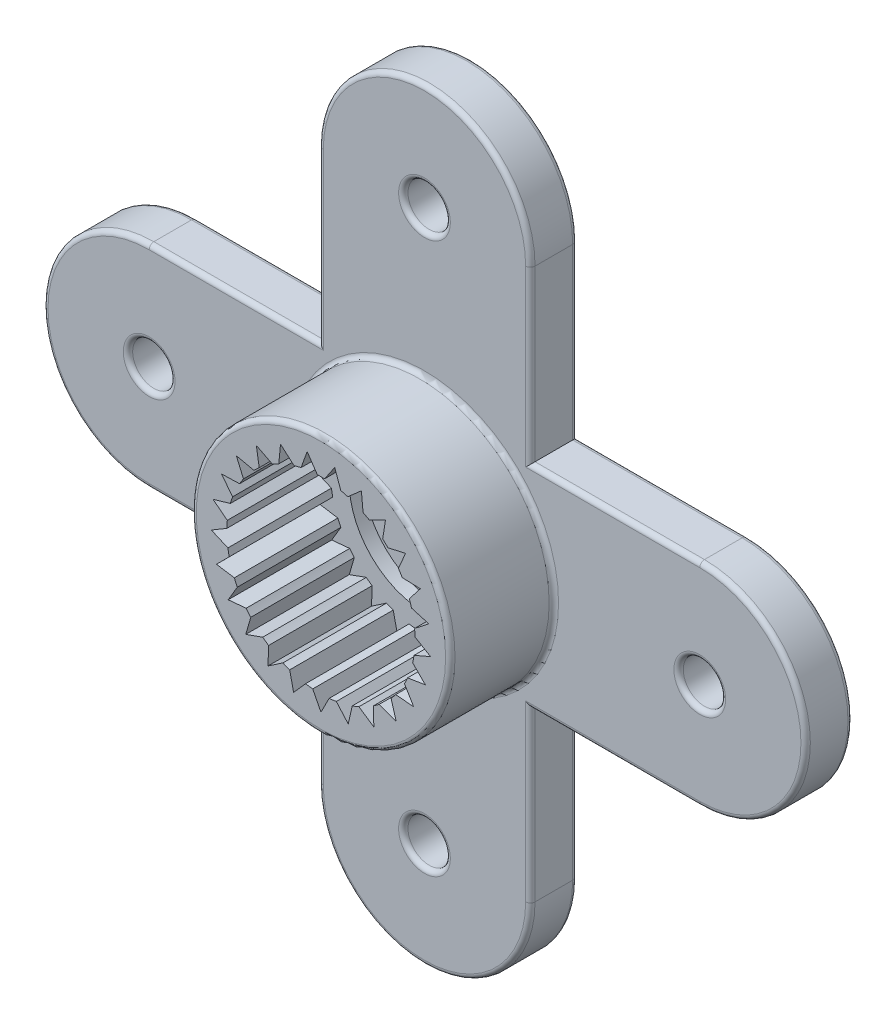
SolidWorks part; units mm, degrees
material "ABS"
ref_plane "Plan de face" through (0, 0, 0) normal (0, 0, 1) x (1, 0, 0)
ref_plane "Plan de dessus" through (0, 0, 0) normal (0, 1, 0) x (1, 0, 0)
ref_plane "Plan de droite" through (0, 0, 0) normal (1, 0, 0) x (0, 0, -1)
sketch "Esquisse1" plane through (0, 0, 0) normal (0, 0, 1) x (1, 0, 0)
  line L0 (-25.8199, 1.564) -> (18.3852, 1.564) construction
  line L1 (0, 0) -> (0, 5.85) construction
  line L2 (-2.25, 5.85) -> (-2.25, 1.5811)
  line L3 (2.25, 5.85) -> (2.25, 1.5811)
  line L4 (0, 5.85) -> (0, 8.1) construction
  line L5 (0, 0) -> (0, -2.75) construction
  circle A0 centre (0, 0) radius 2.75
  arc A1 (2.25, 5.85) -> (-2.25, 5.85) centre (0, 5.85) ccw
  dimension "D3" = 4.5
  dimension "D1" = 5.5
  dimension "D2" = 10.85
extrude "Boss.-Extru.1" add sketch "Esquisse1" along normal blind 1 contours L3 A1 L2 A0 | A0
sketch "Esquisse2" plane through (0, 0, 1) normal (0, 0, 1) x (1, 0, 0)
  circle A0 centre (0, 0) radius 2.75
  arc A1 (-2.25, 1.5811) -> (2.25, 1.5811) centre (0, 0) ccw construction
extrude "Boss.-Extru.2" add sketch "Esquisse2" along normal offset from surface (2.2 mm away) 3.2 up to face at (0, 3.1953, 0)
sketch "Esquisse3" plane through (0, 0, 3.2) normal (0, 0, 1) x (1, 0, 0)
  circle A0 centre (0, 0) radius 2
  dimension "D1" = 4
extrude "Enlèv. mat.-Extru.1" cut sketch "Esquisse3" against normal blind 2.5
sketch "Esquisse4" plane through (0, 0, 0) normal (0, 0, -1) x (-1, 0, 0)
  circle A0 centre (0, 0) radius 1.6
  dimension "D1" = 3.2
extrude "Enlèv. mat.-Extru.2" cut sketch "Esquisse4" against normal blind 0.4
sketch "Esquisse5" plane through (0, 0, 0.4) normal (0, 0, -1) x (-1, 0, 0)
  circle A0 centre (0, 0) radius 0.85
  dimension "D1" = 1.7
extrude "Enlèv. mat.-Extru.3" cut sketch "Esquisse5" against normal blind 4.8
sketch "Esquisse6" plane through (0, 0, 0) normal (0, 0, -1) x (-1, 0, 0)
  line L0 (0, 0) -> (0, 8.1) construction
  circle A2 centre (0, 5.85) radius 0.45
  arc A4 (2.25, 5.85) -> (-2.25, 5.85) centre (0, 5.85) ccw construction
  dimension "D1" = 0.9
extrude "Enlèv. mat.-Extru.4" cut sketch "Esquisse6" against normal through all
sketch "Sketch6" plane through (0, 0, 0) normal (0, 0, -1) x (-1, 0, 0)
  line L0 (0, 8.1) -> (0, 0) construction
  arc A0 (2.25, 5.85) -> (-2.25, 5.85) centre (0, 5.85) ccw construction
  circle A1 centre (0, 3.35) radius 0.45
  circle A2 centre (0, 5.85) radius 0.45 construction
  dimension "D1" = 2.5
extrude "Cut-Extrude3" [suppressed] cut sketch "Sketch6" against normal through all
sketch "Sketch7" [suppressed] plane through (0, 0, 0) normal (0, 0, -1) x (-1, 0, 0)
  line L0 (0, 15.65) -> (0, 0) construction
  arc A0 (2.25, 13.4) -> (-2.25, 13.4) centre (0, 13.4) ccw construction
  circle A1 centre (0, 8.4) radius 0.45
  circle A2 centre (0, 10.9) radius 0.45 construction
  dimension "D1" = 2.5
extrude "Cut-Extrude4" [suppressed] cut sketch "Sketch7" against normal through all contours A1
sketch "Sketch1" plane through (0, 0, 3.2) normal (0, 0, 1) x (1, 0, 0)
  line L0 (0, 0) -> (0, -2) construction
  line L1 (0, 0) -> (0.1743, -1.9924) construction
  line L2 (0, 0) -> (-0.1743, -1.9924) construction
  line L3 (0.1743, -1.9924) -> (0, -2.334)
  line L4 (0, -2.334) -> (-0.1743, -1.9924)
  circle A0 centre (0, 0) radius 2 construction
  circle A1 centre (0, 0) radius 2 construction
  arc A2 (-0.1743, -1.9924) -> (0.1743, -1.9924) centre (0, 0) ccw
  circle A3 centre (0, 0) radius 2.334 construction
  dimension "D3" = 4.668
  dimension "D1" = 5
  dimension "D2" = 5
extrude "Cut-Extrude1" cut sketch "Sketch1" against normal up to surface (2.5 mm away) contours L4 A2 L3 up to face at (0.85, 0, 0.7)
pattern_circular "CirPattern1" count 25 over 360 about axis through (0, 0, 0) along (0, 0, 1) of "Cut-Extrude1"
fillet "Fillet6" [suppressed] radius 0.1
sketch "Sketch2" plane through (0, 0, 0) normal (0, 0, -1) x (-1, 0, 0)
  line L0 (2.25, -1.5811) -> (2.25, -5.85)
  line L1 (-2.25, -1.5811) -> (-2.25, -5.85)
  line L2 (2.25, 5.85) -> (2.25, 1.5811) construction
  line L3 (-2.25, 5.85) -> (-2.25, 1.5811) construction
  line L4 (0, -2.75) -> (0, -8.1) construction
  arc A0 (2.25, -5.85) -> (-2.25, -5.85) centre (0, -5.85) cw
  arc A1 (-2.25, 1.5811) -> (2.25, 1.5811) centre (0, 0) ccw construction
  arc A2 (-2.25, -1.5811) -> (2.25, -1.5811) centre (0, 0) ccw
extrude "Boss-Extrude1" add sketch "Sketch2" against normal up to surface (1 mm away) contours L0 A0 L1 A2 up to face at (0.45, 5.85, 1)
sketch "Sketch3" plane through (0, 0, 0) normal (0, 0, -1) x (-1, 0, 0)
  line L0 (0, -8.1) -> (0, 0) construction
  circle A2 centre (0, -5.85) radius 0.45
  arc A3 (-2.25, -5.85) -> (2.25, -5.85) centre (0, -5.85) ccw construction
  dimension "D3" = 0.9
extrude "Cut-Extrude2" cut sketch "Sketch3" against normal through all
sketch "Sketch8" plane through (0, 0, 0) normal (0, 0, -1) x (-1, 0, 0)
  line L0 (0, -8.1) -> (0, 0) construction
  circle A0 centre (0, -3.35) radius 0.45
  arc A1 (-2.25, -5.85) -> (2.25, -5.85) centre (0, -5.85) ccw construction
  circle A2 centre (0, -5.85) radius 0.45 construction
  dimension "D1" = 2.5
extrude "Cut-Extrude5" [suppressed] cut sketch "Sketch8" against normal through all
sketch "Sketch4" [suppressed] plane through (0, 0, 0) normal (0, 0, -1) x (-1, 0, 0)
  line L0 (2.75, 0) -> (2.2484, -13.4836)
  line L2 (-2.2484, -13.4836) -> (-2.75, 0)
  line L3 (-2.75, 0) -> (-2.2484, 13.4836)
  line L5 (2.2484, 13.4836) -> (2.75, 0)
  line L8 (-2.25, 13.4) -> (-2.25, 1.5811)
  line L9 (-2.25, -1.5811) -> (-2.25, -13.4)
  line L10 (2.25, -13.4) -> (2.25, -1.5811)
  line L11 (2.25, 1.5811) -> (2.25, 13.4)
  line L12 (-2.25, 13.4) -> (-2.25, 1.5811)
  line L13 (-2.25, -1.5811) -> (-2.25, -13.4)
  line L14 (2.25, -13.4) -> (2.25, -1.5811)
  line L15 (2.25, 1.5811) -> (2.25, 13.4)
  arc A0 (2.25, -1.5811) -> (2.25, 1.5811) centre (0, 0) ccw construction
  arc A1 (-2.25, -13.4) -> (2.25, -13.4) centre (0, -13.4) ccw construction
  arc A2 (-2.25, 1.5811) -> (-2.25, -1.5811) centre (0, 0) ccw construction
  arc A3 (2.25, 13.4) -> (-2.25, 13.4) centre (0, 13.4) ccw construction
  arc A4 (-2.2484, 13.4836) -> (-2.25, 13.4) centre (0, 13.4) ccw
  arc A5 (2.2484, -13.4836) -> (2.25, -13.4) centre (0, -13.4) ccw
  arc A8 (-2.25, 1.5811) -> (-2.25, -1.5811) centre (0, 0) ccw
  arc A9 (-2.25, -13.4) -> (2.25, -13.4) centre (0, -13.4) ccw
  arc A10 (2.25, -1.5811) -> (2.25, 1.5811) centre (0, 0) ccw
  arc A11 (2.25, 13.4) -> (-2.25, 13.4) centre (0, 13.4) ccw
  arc A12 (-2.25, 1.5811) -> (-2.25, -1.5811) centre (0, 0) ccw
  arc A13 (-2.25, -13.4) -> (-2.2484, -13.4836) centre (0, -13.4) ccw
  arc A14 (2.25, -1.5811) -> (2.25, 1.5811) centre (0, 0) ccw
  arc A15 (2.25, 13.4) -> (2.2484, 13.4836) centre (0, 13.4) ccw
  line M20 (-2.25, 13.4) -> (-2.25, 1.5811)
  arc M21 (-2.25, 1.5811) -> (-2.25, -1.5811) centre (0, 0) ccw
  line M22 (-2.25, -1.5811) -> (-2.25, -13.4)
  arc M23 (-2.25, -13.4) -> (2.25, -13.4) centre (0, -13.4) ccw
  line M24 (2.25, -13.4) -> (2.25, -1.5811)
  arc M25 (2.25, -1.5811) -> (2.25, 1.5811) centre (0, 0) ccw
  line M26 (2.25, 1.5811) -> (2.25, 13.4)
  arc M27 (2.25, 13.4) -> (-2.25, 13.4) centre (0, 13.4) ccw
  dimension "D1" = 0
extrude "Boss-Extrude2" [suppressed] add sketch "Sketch4" against normal up to surface (1 mm away) contours L2 M23 M22 M21 | L3 M21 M20 M27 | L5 M27 M26 M25 | L0 M25 M24 M23
sketch "Sketch10" [suppressed] plane through (0, 0, 0) normal (0, 0, -1) x (-1, 0, 0)
  line L0 (-2.75, 0) -> (2.75, 0) construction
  line L1 (0, 0) -> (0, 15.65) construction
  circle A0 centre (0, 8.4) radius 0.45
  circle A1 centre (0, 5.9) radius 0.45
  circle A3 centre (0, 10.9) radius 0.45 construction
  arc A4 (-2.7424, 0.2043) -> (-2.7424, -0.2043) centre (0, 0) ccw construction
  arc A5 (2.7424, -0.2043) -> (2.7424, 0.2043) centre (0, 0) ccw construction
  arc A6 (2.2484, 13.4836) -> (-2.2484, 13.4836) centre (0, 13.4) ccw construction
  circle A8 centre (0, -5.9) radius 0.45
  circle A9 centre (0, -8.4) radius 0.45
  dimension "D1" = 2.5
  dimension "D2" = 2.5
extrude "Cut-Extrude7" [suppressed] cut sketch "Sketch10" against normal through all
fillet "Fillet3" [suppressed] radius 0.1
sketch "Sketch5" plane through (0, 0, 0) normal (0, 0, -1) x (-1, 0, 0)
  line L0 (5.85, 2.25) -> (-5.85, 2.25)
  line L1 (-5.85, -2.25) -> (5.85, -2.25)
  line L2 (8.1, 0) -> (-8.1, 0) construction
  arc A0 (5.85, 2.25) -> (5.85, -2.25) centre (5.85, 0) cw
  arc A1 (-5.85, -2.25) -> (-5.85, 2.25) centre (-5.85, 0) cw
  circle A2 centre (0, 0) radius 1.6 construction
  circle A3 centre (0, 0) radius 1.6
  dimension "D1" = 2.25
  dimension "D2" = 16.2
extrude "Boss-Extrude3" add sketch "Sketch5" against normal up to surface (1 mm away) up to face at (0.45, -5.85, 1)
sketch "Sketch9" plane through (0, 0, 0) normal (0, 0, -1) x (-1, 0, 0)
  line L0 (8.1, 0) -> (-8.1, 0) construction
  arc A0 (5.85, -2.25) -> (5.85, 2.25) centre (5.85, 0) ccw construction
  arc A1 (-5.85, 2.25) -> (-5.85, -2.25) centre (-5.85, 0) ccw construction
  circle A2 centre (5.85, 0) radius 0.45
  circle A3 centre (-5.85, 0) radius 0.45
  circle A5 centre (0, -5.85) radius 0.45 construction
extrude "Cut-Extrude6" cut sketch "Sketch9" against normal through all
fillet "Fillet5" radius 0.1 35 edges at (2.75, 0, 1) (2.75, 0, 3.2) (-1.6, 0, 0) (0, -8.1, 1) (0, -8.1, 0) (0.45, -5.85, 1) (-0.45, -5.85, 0) (-2.25, -4.05, 1) (-2.25, -4.05, 0) (2.25, -4.05, 1) (2.25, -4.05, 0) (0.45, 5.85, 1) (-0.45, 5.85, 0) (-4.05, 2.25, 1) (4.05, 2.25, 1) (-4.05, -2.25, 1) (-4.05, 2.25, 0) (-4.05, -2.25, 0) (-8.1, 0, 0) (-8.1, 0, 1) (4.05, -2.25, 1) (8.1, 0, 1) (4.05, 2.25, 0) (8.1, 0, 0) (4.05, -2.25, 0) (-5.4, 0, 1) (-6.3, 0, 0) (6.3, 0, 1) (5.4, 0, 0) (-2.25, 4.05, 0) (0, 8.1, 0) (2.25, 4.05, 0) (0, 8.1, 1)
fillet "Fillet1" [suppressed] radius 0.1
fillet "Fillet2" [suppressed] radius 0.1
fillet "Fillet4" [suppressed] radius 0.1
equation "\"D3@Sketch3\"=\"D1@Esquisse6\""
equation "\"D2@Sketch1\"=\"D1@Sketch1\""
equation "\"D1@Sketch5\"=\"D3@Esquisse1\"/2"
equation "\"D1@Sketch7\"=\"D1@Sketch6\""
equation "\"D1@Fillet2\"=\"D1@Fillet1\""
equation "\"D1@Fillet4\"=\"D1@Fillet1\""
equation "\"D1@Sketch10\"=\"D1@Sketch6\""
equation "\"D2@Sketch10\"=\"D1@Sketch10\""
